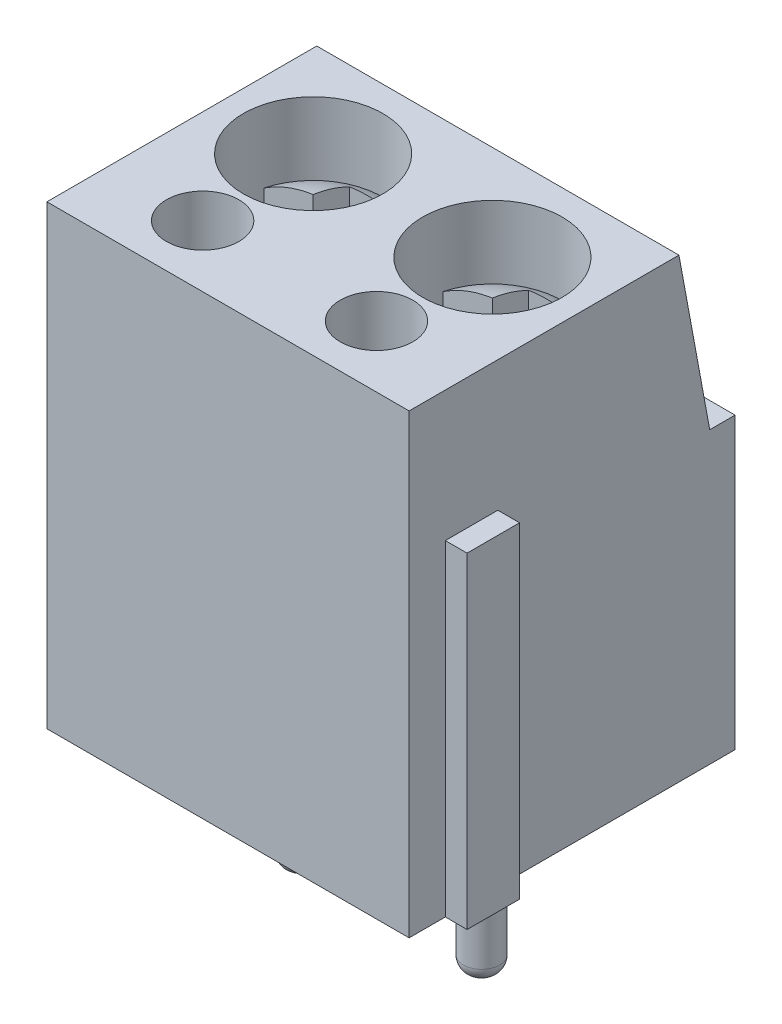
SolidWorks part; units mm, degrees
ref_plane "Plano frontal" through (0, 0, 0) normal (0, 0, 1) x (1, 0, 0)
ref_plane "Plano superior" through (0, 0, 0) normal (0, 1, 0) x (1, 0, 0)
ref_plane "Plano direito" through (0, 0, 0) normal (1, 0, 0) x (0, 0, -1)
sketch "Sketch1" plane through (0, 0, 0) normal (1, 0, 0) x (0, 0, -1)
  line L0 (0, 0) -> (0, 12.6)
  line L1 (0, 12.6) -> (7.45, 12.6)
  line L2 (7.45, 12.6) -> (8.3, 8)
  line L3 (8.3, 8) -> (9, 8)
  line L4 (9, 8) -> (9, 0)
  line L5 (9, 0) -> (0, 0)
  dimension "D1" = 12.6
  dimension "D2" = 7.45
  dimension "D3" = 9
  dimension "D4" = 8
  dimension "D5" = 0.7
extrude "Boss-Extrude1" add sketch "Sketch1" along normal blind 10
sketch "Sketch2" plane through (0, 0, -9) normal (0, 0, -1) x (-1, 0, 0)
  line L0 (0, 0) -> (0, 8) construction
  line L1 (-9.5, 7) -> (-5.5, 7)
  line L2 (-9.5, 7) -> (-9.5, 1)
  line L3 (-9.5, 1) -> (-5.5, 1)
  line L4 (-5.5, 7) -> (-5.5, 1)
  line L5 (-4.5, 7) -> (-0.5, 7)
  line L6 (-4.5, 7) -> (-4.5, 1)
  line L7 (-4.5, 1) -> (-0.5, 1)
  line L8 (-0.5, 7) -> (-0.5, 1)
  line L9 (-10, 0) -> (-10, 8) construction
  line L10 (-10, 0) -> (0, 0) construction
  line L11 (-10, 8) -> (0, 8) construction
  dimension "D1" = 0.5
  dimension "D2" = 1
  dimension "D3" = 0.5
  dimension "D4" = 1
  dimension "D5" = 1
extrude "Cut-Extrude1" cut sketch "Sketch2" against normal blind 2
sketch "Sketch3" plane through (0, 0, -9) normal (0, 0, -1) x (-1, 0, 0)
  line L0 (-9.5, 1) -> (-5.5, 1) construction
  line L1 (-8, 1) -> (-7, 1)
  line L2 (-8, 1) -> (-8, 0)
  line L3 (-8, 0) -> (-7, 0)
  line L4 (-7, 1) -> (-7, 0)
  line L5 (-10, 0) -> (0, 0) construction
  line L6 (-4.5, 1) -> (-0.5, 1) construction
  line L7 (-3, 1) -> (-2, 1)
  line L8 (-3, 1) -> (-3, 0)
  line L9 (-3, 0) -> (-2, 0)
  line L10 (-2, 1) -> (-2, 0)
  line L11 (0, 0) -> (0, 8) construction
  line L12 (-10, 0) -> (-10, 8) construction
  dimension "D1" = 2
  dimension "D2" = 2
  dimension "D3" = 4
extrude "Cut-Extrude2" cut sketch "Sketch3" against normal blind 5
sketch "Sketch4" plane through (0, 0, -7) normal (0, 0, -1) x (-1, 0, 0)
  line L1 (-3, 1) -> (-2, 1) construction
  line L2 (-5.5, 7) -> (-9.5, 7) construction
  line L3 (-0.5, 7) -> (-4.5, 7) construction
  circle A0 centre (-7.5, 3.5) radius 1.5
  circle A1 centre (-2.5, 3.5) radius 1.5
  point P8 (-7.5, 7)
  point P11 (-2.5, 7)
  dimension "D1" = 3
  dimension "D2" = 1
extrude "Cut-Extrude3" cut sketch "Sketch4" against normal blind 5
sketch "Sketch6" plane through (0, 0, -7) normal (0, 0, -1) x (-1, 0, 0)
  line L0 (-9.5, 7) -> (-8.5, 4)
  line L1 (-8.5, 4) -> (-6.5, 4)
  line L2 (-6.5, 4) -> (-5.5, 7)
  line L3 (-5.5, 7) -> (-9.5, 7)
  line L4 (-5.5, 7) -> (-4.5, 7) construction
  line L5 (-5, 7) -> (-5, 0.9151) construction
  line L6 (-4.5, 7) -> (-0.5, 7)
  line L7 (-3.5, 4) -> (-4.5, 7)
  line L8 (-1.5, 4) -> (-3.5, 4)
  line L9 (-0.5, 7) -> (-1.5, 4)
  dimension "D1" = 3
  dimension "D2" = 2
extrude "Boss-Extrude2" add sketch "Sketch6" along normal blind 0.1
sketch "Sketch7" plane through (0, 1, 0) normal (0, -1, 0) x (1, 0, 0)
  line L6 (2, -4) -> (2, -9) construction
  line L8 (3, -4) -> (3, -9) construction
  line L10 (2, -4) -> (3, -4) construction
  line L13 (8, -4) -> (7, -4) construction
  line L16 (8, -4) -> (8, -9) construction
  line L18 (7, -4) -> (7, -7) construction
  circle A0 centre (2.5, -4.5) radius 0.499
  circle A1 centre (7.5, -4.5) radius 0.499
  dimension "D1" = 0.001
  dimension "D2" = 0.001
  dimension "D3" = 0.001
  dimension "D4" = 0.001
  dimension "D5" = 0.001
  dimension "D6" = 0.001
extrude "Boss-Extrude5" add sketch "Sketch7" along normal blind 5.3
sketch "Sketch8" plane through (0, 0, 0) normal (-1, 0, 0) x (0, 0, 1)
  line L0 (0, 0) -> (-9, 0) construction
  line L1 (-2.3, 0) -> (-1, 0)
  line L2 (-2.3, 0) -> (-2.3, 9)
  line L3 (-2.3, 9) -> (-1, 9)
  line L4 (-1, 0) -> (-1, 9)
  line L5 (0, 12.6) -> (0, 0) construction
  dimension "D1" = 1.3
  dimension "D2" = 9
  dimension "D3" = 1
extrude "Cut-Extrude4" cut sketch "Sketch8" against normal blind 0.6
sketch "Sketch9" plane through (10, 0, 0) normal (1, 0, 0) x (0, 0, -1)
  line L0 (0, 0) -> (9, 0) construction
  line L1 (1, 0) -> (2.45, 0)
  line L2 (1, 0) -> (1, 9)
  line L3 (1, 9) -> (2.45, 9)
  line L4 (2.45, 0) -> (2.45, 9)
  line L5 (0, 12.6) -> (0, 0) construction
  dimension "D1" = 1
  dimension "D2" = 1.45
  dimension "D3" = 9
extrude "Boss-Extrude6" add sketch "Sketch9" along normal blind 0.6
sketch "Sketch10" plane through (0, 12.6, 0) normal (0, 1, 0) x (1, 0, 0)
  line L3 (0, 7.45) -> (0, 0) construction
  line L6 (10, 0) -> (0, 0) construction
  line L8 (10, 7.45) -> (0, 7.45) construction
  line L9 (5, 7.45) -> (5, 0) construction
  circle A0 centre (2.525, 4.825) radius 1.925
  circle A1 centre (7.4, 1.7) radius 1
  circle A2 centre (2.6, 1.7) radius 1
  circle A3 centre (7.475, 4.825) radius 1.925
  dimension "D1" = 3.85
  dimension "D2" = 2
  dimension "D4" = 0.6
  dimension "D5" = 1.6
  dimension "D7" = 0.7
  dimension "D8" = 0.7
extrude "Cut-Extrude5" cut sketch "Sketch10" against normal blind 2
sketch "Sketch11" plane through (0, 0, -7.1) normal (0, 0, -1) x (-1, 0, 0)
  line L0 (-4.5, 7) -> (-5.5, 7) construction
  line L1 (-8.5, 4) -> (-6.5, 4)
  line L2 (-8.5, 4) -> (-8.5, 3.9)
  line L3 (-8.5, 3.9) -> (-6.5, 3.9)
  line L4 (-6.5, 4) -> (-6.5, 3.9)
  line L5 (-5, 7) -> (-5, 2.7412) construction
  line L6 (-3.5, 4) -> (-3.5, 3.9)
  line L7 (-1.5, 3.9) -> (-3.5, 3.9)
  line L8 (-1.5, 4) -> (-1.5, 3.9)
  line L9 (-1.5, 4) -> (-3.5, 4)
  dimension "D1" = 0.1
extrude "Boss-Extrude7" add sketch "Sketch11" against normal blind 3
fillet "Fillet1" radius 0.1 2 edges at (2.5, 3.9, -7.1) (7.5, 3.9, -7.1)
fillet "Fillet2" radius 0.4 2 edges at (7.5, -4.3, -4.999) (2.5, -4.3, -4.999)
sketch "Sketch12" plane through (0, 10.6, 0) normal (0, 1, 0) x (1, 0, 0)
  line L0 (5.55, 4.825) -> (9.4, 4.825)
  circle A0 centre (7.475, 4.825) radius 1.925 construction
  circle A1 centre (7.475, 4.825) radius 1.925 construction
ref_plane "Plane1" through (0, 0, -4.825) normal (0, 0, 1) x (1, 0, 0)
sketch "Sketch13" plane through (0, 0, -4.825) normal (0, 0, 1) x (1, 0, 0)
  line L0 (7.475, 10.6) -> (7.475, 11.5349) construction
  line L1 (5.55, 10.6) -> (9.4, 10.6) construction
  line L2 (7.475, 11.1979) -> (7.475, 10.6)
  line L3 (7.475, 10.6) -> (9.4, 10.6)
  arc A0 (7.475, 11.1979) -> (9.4, 10.6) centre (7.475, 7.8) cw
revolve "Revolve1" add sketch "Sketch13" angle 360 about L0
ref_plane "Plane2" through (5, 0, 0) normal (1, 0, 0) x (0, 0, -1)
sketch "Sketch15" plane through (0, 12.6, 0) normal (0, 1, 0) x (1, 0, 0)
  line L0 (7.475, 6.75) -> (7.475, 2.9) construction
  line L1 (6.975, 6.325) -> (7.975, 6.325)
  line L2 (6.975, 6.325) -> (6.975, 3.325)
  line L3 (6.975, 3.325) -> (7.975, 3.325)
  line L4 (7.975, 6.325) -> (7.975, 3.325)
  line L5 (5.6161, 5.325) -> (9.3339, 5.325)
  line L7 (5.6161, 4.325) -> (9.3339, 4.325)
  line L10 (9.4, 4.825) -> (5.55, 4.825) construction
  arc A0 (5.6161, 5.325) -> (5.6161, 4.325) centre (7.475, 4.825) ccw
  circle A1 centre (7.475, 4.825) radius 1.925 construction
  circle A2 centre (7.475, 4.825) radius 1.925 construction
  arc A3 (9.3339, 4.325) -> (9.3339, 5.325) centre (7.475, 4.825) ccw
  point P4 (7.975, 4.825)
  point P5 (7.475, 6.325)
  circle M1 centre (7.475, 4.825) radius 1.925
  dimension "D1" = 1
  dimension "D2" = 1
  dimension "D3" = 3
  dimension "D4" = 0.5
extrude "Cut-Extrude6" cut sketch "Sketch15" against normal blind 3 contours L4 L7 L5 M1 | L2 L7 L4 L5 | L2 L5 L4 L1 | L7 L2 L5 M1 | L7 L2 L3 L4
mirror "Mirror1" about plane through (5, 0, 0) normal (1, 0, 0) of "Cut-Extrude6", "Revolve1"
sketch "Sketch16" plane through (0, 10.6, 0) normal (0, 1, 0) x (1, 0, 0)
  circle A1 centre (2.6, 1.7) radius 1
  circle A2 centre (2.6, 1.7) radius 1
  circle A3 centre (7.4, 1.7) radius 1
  circle A4 centre (7.4, 1.7) radius 1
  dimension "D1" = 0
  dimension "D2" = 0
extrude "Cut-Extrude7" cut sketch "Sketch16" against normal blind 3
sketch "Sketch17" plane through (0, 9.6, 0) normal (0, 1, 0) x (1, 0, 0)
  line L10 (2.025, 5.325) -> (0.6661, 5.325)
  line L11 (0.6661, 4.325) -> (2.025, 4.325)
  line L12 (2.025, 4.325) -> (2.025, 3.325)
  line L13 (2.025, 3.325) -> (3.025, 3.325)
  line L14 (3.025, 3.325) -> (3.025, 4.325)
  line L15 (3.025, 4.325) -> (4.3839, 4.325)
  line L16 (4.3839, 5.325) -> (3.025, 5.325)
  line L17 (3.025, 5.325) -> (3.025, 6.325)
  line L18 (3.025, 6.325) -> (2.025, 6.325)
  line L19 (2.025, 6.325) -> (2.025, 5.325)
  line L20 (2.025, 5.325) -> (0.6661, 5.325)
  line L21 (0.6661, 4.325) -> (2.025, 4.325)
  line L22 (2.025, 4.325) -> (2.025, 3.325)
  line L23 (2.025, 3.325) -> (3.025, 3.325)
  line L24 (3.025, 3.325) -> (3.025, 4.325)
  line L25 (3.025, 4.325) -> (4.3839, 4.325)
  line L26 (4.3839, 5.325) -> (3.025, 5.325)
  line L27 (3.025, 5.325) -> (3.025, 6.325)
  line L28 (3.025, 6.325) -> (2.025, 6.325)
  line L29 (2.025, 6.325) -> (2.025, 5.325)
  line L30 (9.3339, 5.325) -> (7.975, 5.325)
  line L31 (7.975, 5.325) -> (7.975, 6.325)
  line L32 (7.975, 6.325) -> (6.975, 6.325)
  line L33 (6.975, 6.325) -> (6.975, 5.325)
  line L34 (6.975, 5.325) -> (5.6161, 5.325)
  line L35 (5.6161, 4.325) -> (6.975, 4.325)
  line L36 (6.975, 4.325) -> (6.975, 3.325)
  line L37 (6.975, 3.325) -> (7.975, 3.325)
  line L38 (7.975, 3.325) -> (7.975, 4.325)
  line L39 (7.975, 4.325) -> (9.3339, 4.325)
  line L40 (9.3339, 5.325) -> (7.975, 5.325)
  line L41 (7.975, 5.325) -> (7.975, 6.325)
  line L42 (7.975, 6.325) -> (6.975, 6.325)
  line L43 (6.975, 6.325) -> (6.975, 5.325)
  line L44 (6.975, 5.325) -> (5.6161, 5.325)
  line L45 (5.6161, 4.325) -> (6.975, 4.325)
  line L46 (6.975, 4.325) -> (6.975, 3.325)
  line L47 (6.975, 3.325) -> (7.975, 3.325)
  line L48 (7.975, 3.325) -> (7.975, 4.325)
  line L49 (7.975, 4.325) -> (9.3339, 4.325)
  arc A2 (0.6661, 5.325) -> (0.6661, 4.325) centre (2.525, 4.825) ccw
  arc A3 (4.3839, 4.325) -> (4.3839, 5.325) centre (2.525, 4.825) ccw
  arc A4 (0.6661, 5.325) -> (0.6661, 4.325) centre (2.525, 4.825) ccw
  arc A5 (4.3839, 4.325) -> (4.3839, 5.325) centre (2.525, 4.825) ccw
  arc A6 (5.6161, 5.325) -> (5.6161, 4.325) centre (7.475, 4.825) ccw
  arc A7 (9.3339, 4.325) -> (9.3339, 5.325) centre (7.475, 4.825) ccw
  arc A8 (5.6161, 5.325) -> (5.6161, 4.325) centre (7.475, 4.825) ccw
  arc A9 (9.3339, 4.325) -> (9.3339, 5.325) centre (7.475, 4.825) ccw
  dimension "D1" = 0
  dimension "D2" = 0
extrude "Cut-Extrude8" cut sketch "Sketch17" against normal blind 1 draft 20
